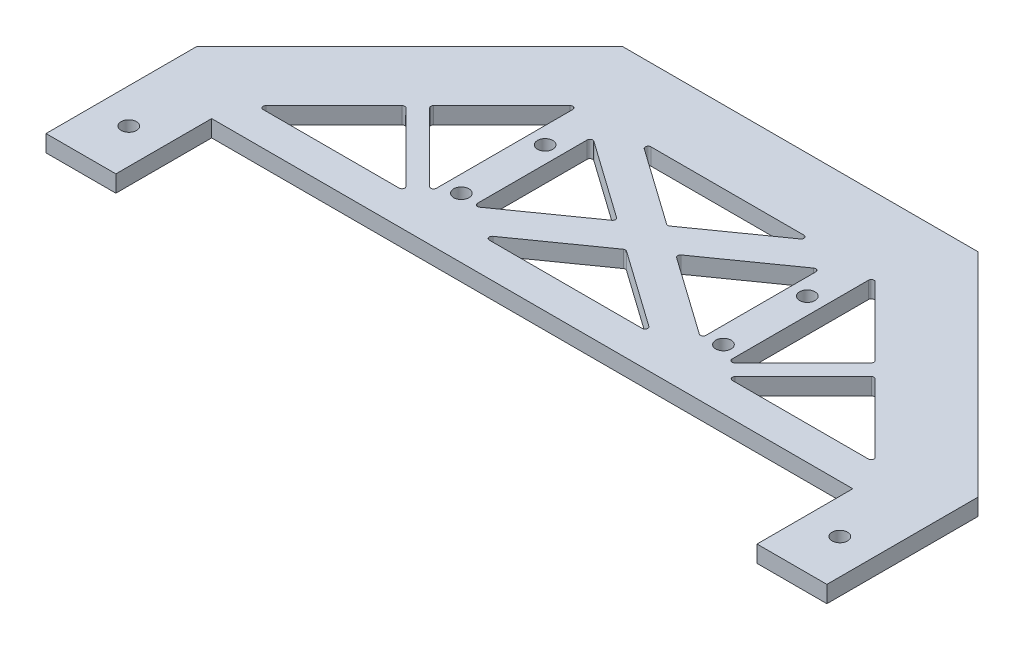
SolidWorks part; units mm, degrees
ref_plane "Front" through (0, 0, 0) normal (0, 0, 1) x (1, 0, 0)
ref_plane "Top" through (0, 0, 0) normal (0, 1, 0) x (1, 0, 0)
ref_plane "Right" through (0, 0, 0) normal (1, 0, 0) x (0, 0, -1)
sketch "Sketch1" plane through (0, 0, 0) normal (0, 1, 0) x (1, 0, 0)
  line L0 (12.5, 17.135) -> (127.2, 17.135)
  line L1 (0, 0) -> (12.5, 0)
  line L2 (0, 0) -> (0, 17.135)
  line L4 (12.5, 0) -> (12.5, 17.135)
  line L5 (139.7, 17.135) -> (139.7, 0)
  line L6 (139.7, 0) -> (127.2, 0)
  line L7 (127.2, 0) -> (127.2, 17.135)
  line L8 (0, 17.135) -> (0, 27.0345)
  line L9 (139.7, 17.135) -> (139.7, 27.0345)
  line L10 (38.0177, 65.0522) -> (101.6823, 65.0522)
  line L11 (0, 27.0345) -> (38.0177, 65.0522)
  line L12 (101.6823, 65.0522) -> (139.7, 27.0345)
  line L13 (55.8831, 24.0432) -> (69.5613, 33.7152)
  line L14 (56.1717, 23.135) -> (83.5283, 23.135)
  line L15 (49.4025, 27.7752) -> (49.4025, 47.412)
  line L16 (56.1717, 52.0522) -> (83.5283, 52.0522)
  line L17 (90.2975, 27.7752) -> (90.2975, 47.412)
  line L18 (49.4025, 23.135) -> (90.2975, 52.0522) construction
  line L19 (49.4025, 52.0522) -> (90.2975, 23.135) construction
  line L20 (50.1911, 47.8203) -> (64.0765, 38.0018)
  line L21 (50.1911, 27.3669) -> (64.0765, 37.1853)
  line L22 (55.8831, 51.1439) -> (69.5613, 41.472)
  line L23 (51.1345, 54.5017) -> (92.0296, 25.5845) construction
  line L24 (47.6704, 49.6027) -> (88.5655, 20.6855) construction
  line L25 (47.6704, 25.5845) -> (88.5655, 54.5017) construction
  line L26 (51.1345, 20.6855) -> (92.0296, 49.6027) construction
  line L27 (70.1387, 41.472) -> (83.8169, 51.1439)
  line L28 (70.1387, 33.7152) -> (83.8169, 24.0432)
  line L29 (75.6235, 38.0018) -> (89.5089, 47.8203)
  line L30 (75.6235, 37.1853) -> (89.5089, 27.3669)
  line L31 (69.85, 65.0522) -> (69.85, 91.4111) construction
  line L32 (15.6924, 23.135) -> (40.0478, 23.135)
  line L33 (15.3388, 23.9886) -> (27.5165, 36.1662)
  line L34 (28.2236, 36.1662) -> (40.4013, 23.9886)
  line L35 (30.345, 38.9947) -> (42.5489, 51.1986)
  line L36 (30.345, 38.2876) -> (42.5489, 26.0836)
  line L37 (43.4025, 50.8451) -> (43.4025, 26.4372)
  line L38 (109.355, 38.9947) -> (97.1511, 51.1986)
  line L39 (109.355, 38.2876) -> (97.1511, 26.0836)
  line L40 (96.2975, 50.8451) -> (96.2975, 26.4372)
  line L41 (124.3612, 23.9886) -> (112.1835, 36.1662)
  line L42 (111.4764, 36.1662) -> (99.2987, 23.9886)
  line L43 (124.0076, 23.135) -> (99.6522, 23.135)
  arc A0 (50.1911, 27.3669) -> (49.4025, 27.7752) centre (49.9025, 27.7752) cw
  arc A1 (64.0765, 37.1853) -> (64.0765, 38.0018) centre (63.7878, 37.5936) ccw
  arc A2 (49.4025, 47.412) -> (50.1911, 47.8203) centre (49.9025, 47.412) cw
  arc A3 (55.8831, 51.1439) -> (56.1717, 52.0522) centre (56.1717, 51.5522) cw
  arc A4 (83.8169, 51.1439) -> (83.5283, 52.0522) centre (83.5283, 51.5522) ccw
  arc A5 (70.1387, 41.472) -> (69.5613, 41.472) centre (69.85, 41.8802) cw
  arc A6 (90.2975, 47.412) -> (89.5089, 47.8203) centre (89.7975, 47.412) ccw
  arc A7 (75.6235, 37.1853) -> (75.6235, 38.0018) centre (75.9122, 37.5936) cw
  arc A8 (89.5089, 27.3669) -> (90.2975, 27.7752) centre (89.7975, 27.7752) ccw
  arc A9 (83.8169, 24.0432) -> (83.5283, 23.135) centre (83.5283, 23.635) cw
  arc A10 (70.1387, 33.7152) -> (69.5613, 33.7152) centre (69.85, 33.307) ccw
  arc A11 (55.8831, 24.0432) -> (56.1717, 23.135) centre (56.1717, 23.635) ccw
  arc A12 (42.5489, 51.1986) -> (43.4025, 50.8451) centre (42.9025, 50.8451) cw
  arc A13 (30.345, 38.9947) -> (30.345, 38.2876) centre (30.6985, 38.6411) ccw
  arc A14 (42.5489, 26.0836) -> (43.4025, 26.4372) centre (42.9025, 26.4372) ccw
  arc A15 (40.4013, 23.9886) -> (40.0478, 23.135) centre (40.0478, 23.635) cw
  arc A16 (27.5165, 36.1662) -> (28.2236, 36.1662) centre (27.8701, 35.8127) cw
  arc A17 (15.6924, 23.135) -> (15.3388, 23.9886) centre (15.6924, 23.635) cw
  arc A18 (109.355, 38.9947) -> (109.355, 38.2876) centre (109.0015, 38.6411) cw
  arc A19 (97.1511, 51.1986) -> (96.2975, 50.8451) centre (96.7975, 50.8451) ccw
  arc A20 (97.1511, 26.0836) -> (96.2975, 26.4372) centre (96.7975, 26.4372) cw
  arc A21 (112.1835, 36.1662) -> (111.4764, 36.1662) centre (111.8299, 35.8127) ccw
  arc A22 (99.2987, 23.9886) -> (99.6522, 23.135) centre (99.6522, 23.635) ccw
  arc A23 (124.0076, 23.135) -> (124.3612, 23.9886) centre (124.0076, 23.635) ccw
  circle A24 centre (6.25, 8.5675) radius 1.375
  circle A25 centre (133.45, 8.5675) radius 1.375
  circle A26 centre (46.4025, 27.8946) radius 1.375
  circle A27 centre (46.4025, 42.8946) radius 1.375
  circle A28 centre (93.2975, 27.8946) radius 1.375
  circle A29 centre (93.2975, 42.8946) radius 1.375
  point P5 (69.85, 17.135)
  point P14 (69.85, 65.0522)
  point P15 (69.85, 37.5936)
  point P74 (43.4025, 52.0522)
  point P77 (29.9914, 38.6411)
  point P80 (43.4025, 25.2301)
  point P83 (41.2549, 23.135)
  point P86 (27.8701, 36.5198)
  point P89 (14.4853, 23.135)
  point P110 (6.25, 0)
  dimension "D12" = 0.5
  dimension "D19" = 0.5
  dimension "D20" = 2.75
  dimension "D22" = 2.75
  dimension "D1" = 12.5
  dimension "D2" = 17.135
  dimension "D3" = 139.7
  dimension "D4" = 9.8995
  dimension "D5" = 47.9172
  dimension "D6" = 63.6646
  dimension "D7" = 28.9172
  dimension "D8" = 40.8951
  dimension "D9" = 6
  dimension "D13" = 26.7696
  dimension "D14" = 6
  dimension "D15" = 13
  dimension "D16" = 18.9661
  dimension "D17" = 3
  dimension "D18" = 18.9661
  dimension "D21" = 8.5675
  dimension "D23" = 15
  dimension "D24" = 3
  dimension "D25" = 10.7596
  dimension "D10" = 3
  dimension "D11" = 3
extrude "Boss-Extrude1" add sketch "Sketch1" along normal blind 3
